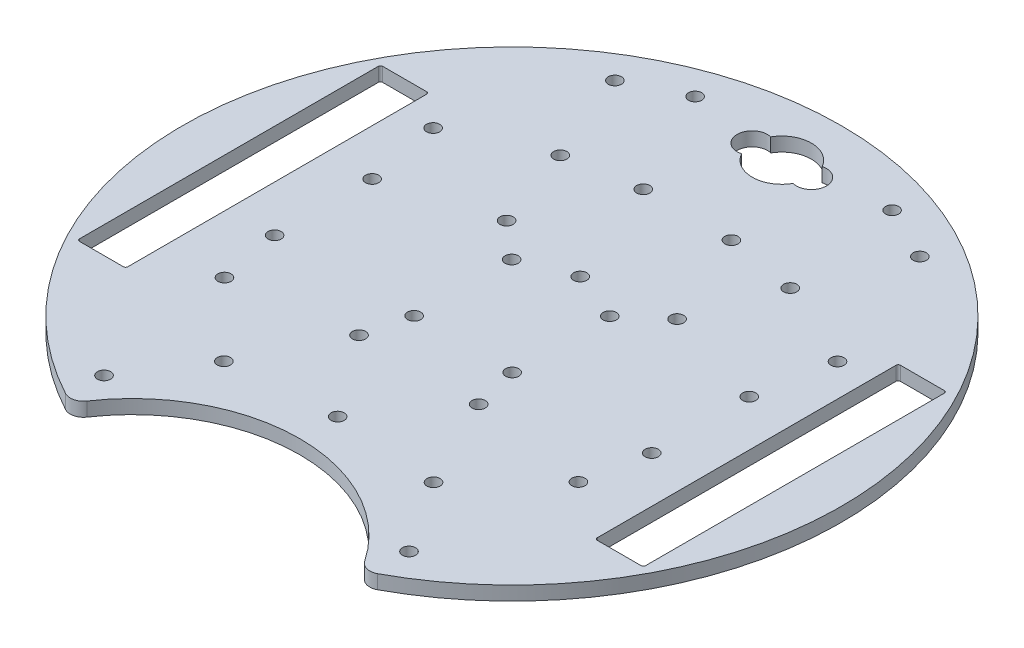
SolidWorks part; units mm, degrees
ref_plane "Front Plane" through (0, 0, 0) normal (0, 0, 1) x (1, 0, 0)
ref_plane "Top Plane" through (0, 0, 0) normal (0, 1, 0) x (1, 0, 0)
ref_plane "Right Plane" through (0, 0, 0) normal (1, 0, 0) x (0, 0, -1)
sketch "Sketch1" plane through (0, 0, 0) normal (0, 1, 0) x (1, 0, 0)
  line L0 (0, 0) -> (-51.5062, -59.2511) construction
  line L1 (0, 86.2583) -> (0, -96.8543) construction
  line L2 (-26.1633, 37.1696) -> (-32.2721, 24.2954) construction
  line L3 (-32.9956, -67.352) -> (0, -86.402) construction
  line L4 (32.9956, -67.352) -> (0, -86.402) construction
  line L5 (0, 0) -> (-13.6167, -50.8184) construction
  line L6 (-33.3347, -42.5389) -> (-41.6896, -52.1501) construction
  line L7 (-32.2721, 24.2954) -> (-46.0115, 28.0759) construction
  line L8 (-83.3992, 0) -> (107.0959, 0) construction
  line L9 (53.4101, -34) -> (53.4101, 34)
  line L10 (-63.9101, -34.5) -> (-53.9101, -34.5)
  line L11 (-64.4101, -34) -> (-64.4101, 34)
  line L12 (-63.9101, 34.5) -> (-53.9101, 34.5)
  line L13 (-53.4101, -34) -> (-53.4101, 34)
  line L14 (63.9101, 34.5) -> (53.9101, 34.5)
  line L15 (64.4101, -34) -> (64.4101, 34)
  line L16 (63.9101, -34.5) -> (53.9101, -34.5)
  line L17 (0, 0) -> (13.6167, -50.8184) construction
  line L18 (-33.3347, -42.5389) -> (-37.4856, -38.9306) construction
  line L19 (0, 0) -> (-95.645, -6.6882) construction
  line L20 (-37.4856, -38.9306) -> (-45.4633, -48.1079) construction
  line L21 (-42.5389, 33.3347) -> (-51.7162, 41.3124) construction
  line L22 (33.3347, -42.5389) -> (41.6896, -52.1501) construction
  line L23 (37.4856, -38.9306) -> (45.4633, -48.1079) construction
  line L24 (-38.9306, 37.4856) -> (-42.5389, 33.3347) construction
  line L25 (-38.9306, 37.4856) -> (-48.5418, 45.8405) construction
  line L26 (33.3347, -42.5389) -> (37.4856, -38.9306) construction
  line L27 (38.9306, 37.4856) -> (42.5389, 33.3347) construction
  line L28 (42.5389, 33.3347) -> (51.7162, 41.3124) construction
  line L29 (-18.4555, -45.8919) -> (-23.0541, -33.9225) construction
  line L30 (-23.0541, -33.9225) -> (-17.92, -31.9499) construction
  line L31 (38.9306, 37.4856) -> (48.5418, 45.8405) construction
  line L32 (-58.9101, -34.5) -> (-58.9101, 19.5819) construction
  line L35 (-13.6167, -50.8184) -> (-25.1096, -20.9046) construction
  line L37 (-13.3214, -43.9193) -> (-17.92, -31.9499) construction
  line L38 (13.6167, -50.8184) -> (24.3327, -22.8079) construction
  line L39 (18.4555, -45.8919) -> (23.0541, -33.9225) construction
  line L40 (23.0541, -33.9225) -> (17.92, -31.9499) construction
  line L41 (13.3214, -43.9193) -> (17.92, -31.9499) construction
  line L42 (-58.5537, 0) -> (91.2411, 0) construction
  line L46 (0, 34.6626) -> (0, -51.647) construction
  line L47 (-37.1849, 0) -> (48.113, 0) construction
  line L48 (0, 49.2959) -> (0, -33.0158) construction
  arc A0 (35.4973, -66.0677) -> (-35.4973, -66.0677) centre (0, 0) ccw
  arc A1 (31.59, -65.1022) -> (-31.59, -65.1022) centre (0, -86.402) ccw
  circle A2 centre (0, 0) radius 74 construction
  circle A3 centre (-13.6089, -21.1831) radius 1.5
  circle A4 centre (27.6453, -18.6148) radius 14.218 construction
  arc A5 (40.0385, -63.4186) -> (41.6896, -52.1501) centre (36.0347, -57.0767) ccw construction
  arc A6 (57.2141, -48.4928) -> (45.4633, -48.1079) centre (51.4912, -43.6452) cw construction
  circle A7 centre (27.6453, -18.6148) radius 12.095 construction
  circle A8 centre (-46.0115, 28.0759) radius 1.5
  circle A9 centre (13.6089, -21.1831) radius 1.5
  circle A10 centre (23.8525, -41.6946) radius 1.5
  arc A11 (-57.2141, -48.4928) -> (-45.4633, -48.1079) centre (-51.4912, -43.6452) ccw construction
  arc A12 (-40.0385, -63.4186) -> (-41.6896, -52.1501) centre (-36.0347, -57.0767) cw construction
  arc A13 (-5.2684, -48.6449) -> (-13.3214, -43.9193) centre (-6.3241, -41.2196) cw construction
  arc A14 (-21.2728, -54.7938) -> (-18.4555, -45.8919) centre (-25.4604, -48.5717) ccw construction
  circle A15 centre (-26.2497, -27.6477) radius 12.095 construction
  circle A16 centre (-26.2497, -27.6477) radius 14.25 construction
  arc A17 (21.2728, -54.7938) -> (18.4555, -45.8919) centre (25.4604, -48.5717) cw construction
  arc A18 (5.2684, -48.6449) -> (13.3214, -43.9193) centre (6.3241, -41.2196) ccw construction
  circle A19 centre (-42.9101, 11.1) radius 1.5
  circle A20 centre (-42.9101, -11.1) radius 1.5
  circle A21 centre (-11.1601, -11.1) radius 1.5
  circle A22 centre (-11.1601, 11.1) radius 1.5
  circle A23 centre (11.1601, 11.1) radius 1.5
  circle A24 centre (11.1601, -11.1) radius 1.5
  circle A25 centre (42.9101, -11.1) radius 1.5
  circle A26 centre (42.9101, 11.1) radius 1.5
  circle A27 centre (-23.8525, -41.6946) radius 1.5
  circle A28 centre (19.3979, 18.1866) radius 1.5
  circle A29 centre (0, 29.7936) radius 12.095 construction
  circle A30 centre (0, -25.4092) radius 12.095 construction
  circle A31 centre (-40.2774, -25.1402) radius 1.5
  circle A32 centre (40.2774, -25.1402) radius 1.5
  circle A33 centre (6.731, 61.4226) radius 1.143
  circle A34 centre (-6.731, 61.4226) radius 1.143
  arc A35 (-5.8539, 64.7449) -> (5.8576, 64.7385) centre (0, 61.4226) cw
  arc A36 (5.8576, 64.7385) -> (5.8576, 58.1067) centre (6.731, 61.4226) cw
  arc A37 (-5.8539, 58.1002) -> (-5.8539, 64.7449) centre (-6.731, 61.4226) cw
  arc A38 (5.8576, 58.1067) -> (-5.8539, 58.1002) centre (0, 61.4226) cw
  circle A39 centre (26.2497, -27.6477) radius 14.25 construction
  circle A40 centre (-22.4162, 64.0967) radius 1.5
  circle A41 centre (22.4162, 64.0967) radius 1.5
  circle A42 centre (32.2721, 24.2954) radius 14.25 construction
  circle A43 centre (-32.2721, 24.2954) radius 12.095 construction
  circle A44 centre (26.1633, 37.1696) radius 1.5
  circle A45 centre (32.2721, 24.2954) radius 12.095 construction
  circle A46 centre (-27.6453, -18.6148) radius 12.095 construction
  circle A47 centre (26.2497, -27.6477) radius 12.095 construction
  circle A48 centre (46.0115, 28.0759) radius 1.5
  circle A49 centre (-20.0544, 50.0438) radius 12.095 construction
  circle A50 centre (10.0272, 39.9187) radius 1.5
  arc A51 (-35.4973, -66.0677) -> (-31.59, -65.1022) centre (-34.0774, -63.425) ccw
  arc A52 (35.4973, -66.0677) -> (31.59, -65.1022) centre (34.0774, -63.425) cw
  circle A53 centre (0, -39.6592) radius 1.5
  circle A54 centre (-32.2721, 24.2954) radius 14.25 construction
  circle A55 centre (-10.0272, 39.9187) radius 1.5
  circle A56 centre (20.0544, 50.0438) radius 14.25 construction
  circle A57 centre (20.0544, 50.0438) radius 12.095 construction
  circle A58 centre (0, 29.7936) radius 14.25 construction
  circle A59 centre (-34.6952, -58.123) radius 1.5
  circle A60 centre (-34.6952, 58.123) radius 1.5
  circle A61 centre (34.6952, -58.123) radius 1.5
  circle A62 centre (0, 15.5436) radius 1.5
  circle A63 centre (-26.1633, 37.1696) radius 1.5
  circle A64 centre (0, 0) radius 67.6907 construction
  circle A65 centre (-19.3979, 18.1866) radius 1.5
  circle A66 centre (-20.0544, 50.0438) radius 14.25 construction
  circle A67 centre (34.6952, 58.123) radius 1.5
  arc A68 (-48.475, 57.2291) -> (-48.5418, 45.8405) centre (-43.6275, 51.5062) ccw construction
  arc A69 (-63.4062, 40.0581) -> (-51.7162, 41.3124) centre (-57.0643, 36.0543) cw construction
  arc A70 (63.4062, 40.0581) -> (51.7162, 41.3124) centre (57.0643, 36.0543) ccw construction
  arc A71 (48.475, 57.2291) -> (48.5418, 45.8405) centre (43.6275, 51.5062) cw construction
  arc A72 (-64.4101, -34) -> (-63.9101, -34.5) centre (-63.9101, -34) ccw
  arc A73 (-53.4101, -34) -> (-53.9101, -34.5) centre (-53.9101, -34) cw
  circle A74 centre (-27.6453, -18.6148) radius 14.218 construction
  arc A75 (-53.4101, 34) -> (-53.9101, 34.5) centre (-53.9101, 34) ccw
  arc A76 (-64.4101, 34) -> (-63.9101, 34.5) centre (-63.9101, 34) cw
  arc A77 (64.4101, 34) -> (63.9101, 34.5) centre (63.9101, 34) ccw
  circle A78 centre (0, -25.4092) radius 14.25 construction
  arc A79 (53.4101, 34) -> (53.9101, 34.5) centre (53.9101, 34) cw
  arc A80 (53.4101, -34) -> (53.9101, -34.5) centre (53.9101, -34) ccw
  arc A81 (64.4101, -34) -> (63.9101, -34.5) centre (63.9101, -34) cw
  point P14 (-62.6039, 0)
  point P23 (62.6039, 0)
  point P35 (-31.5178, -45.012)
  point P40 (-46.7211, -26.9744)
  point P45 (-23.8153, 50.3782)
  point P48 (0, -25.4092)
  point P84 (-20.4871, -32.9362)
  point P154 (0, 58.1002)
  dimension "D1" = 150
  dimension "D2" = 76.2
  dimension "D10" = 148
  dimension "D13" = 3
  dimension "D14" = 3
  dimension "D22" = 2.286
  dimension "D20" = 3
  dimension "D11" = 24.19
  dimension "D12" = 28.436
  dimension "D24" = 28.5
  dimension "D21" = 24.19
  dimension "D25" = 28.5
  dimension "D26" = 28.5
  dimension "D29" = 28.5
  dimension "D8" = 28.5
  dimension "D16" = 6
  dimension "D3" = 120
  dimension "D9" = 30
  dimension "D6" = 12.8224
  dimension "D17" = 22.2
  dimension "D19" = 22.2
  dimension "D15" = 10.5
  dimension "D18" = 31.75
  dimension "D23" = 13.462
  dimension "D31" = 100
  dimension "D27" = 45
  dimension "D28" = 12.735
  dimension "D30" = 170
extrude "Boss-Extrude2" add sketch "Sketch1" along normal blind 3.175
fillet "Fillet1" [suppressed] radius 2
equation "\"D10@Sketch1\"=150-2"
